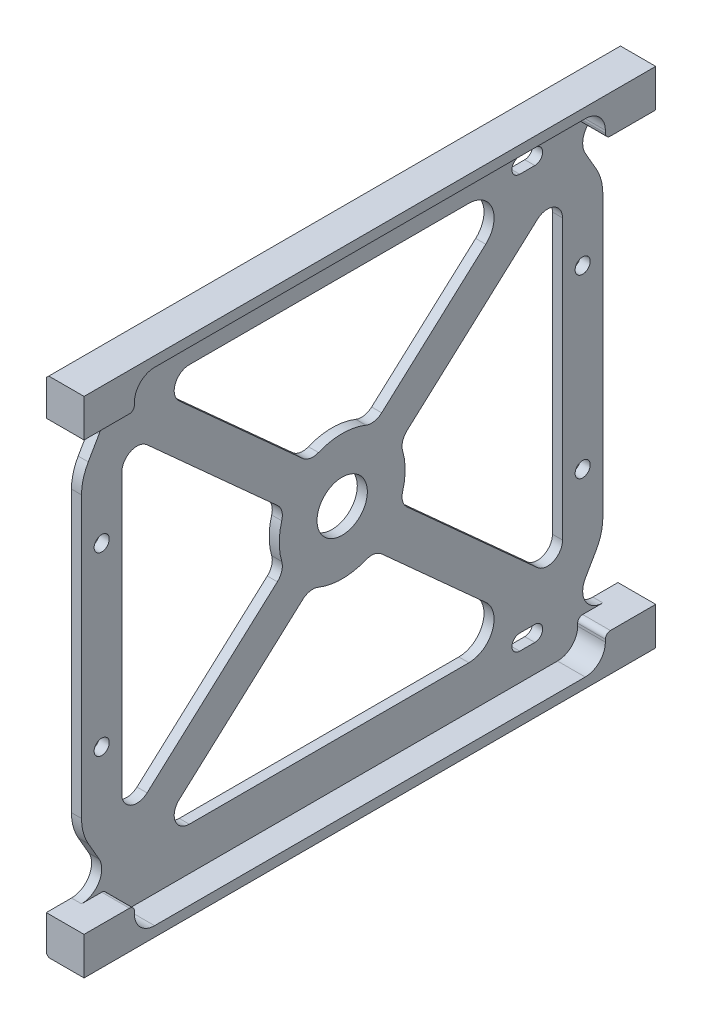
SolidWorks part; units mm, degrees
material "6061-T6 (SS)"
ref_plane "Front Plane" through (0, 0, 0) normal (0, 0, 1) x (1, 0, 0)
ref_plane "Top Plane" through (0, 0, 0) normal (0, 1, 0) x (1, 0, 0)
ref_plane "Right Plane" through (0, 0, 0) normal (1, 0, 0) x (0, 0, -1)
sketch "Sketch1" plane through (0, 0, 0) normal (0, 0, 1) x (1, 0, 0)
  line L0 (0, 50) -> (0, -50)
  line L1 (0, -50) -> (7.5, -50)
  line L2 (7.5, -50) -> (7.5, -42.5)
  line L3 (7.5, -42.5) -> (2, -42.5)
  line L4 (2, -42.5) -> (2, 42.5)
  line L5 (2, 42.5) -> (7.5, 42.5)
  line L6 (7.5, 42.5) -> (7.5, 50)
  line L7 (7.5, 50) -> (0, 50)
  dimension "D1" = 2
  dimension "D2" = 7.5
  dimension "D3" = 7.5
  dimension "D4" = 100
  dimension "D5" = 50
extrude "Boss-Extrude1" add sketch "Sketch1" along normal mid plane 113.5
sketch "Sketch2" plane through (2, 0, 0) normal (1, 0, 0) x (0, 0, -1)
  line L0 (-56.75, -42.5) -> (56.75, -42.5) construction
  line L1 (-56.75, 42.5) -> (-51.75, 42.5)
  line L2 (-56.75, 42.5) -> (-56.75, -42.5)
  line L3 (-56.75, -42.5) -> (-51.75, -42.5)
  line L4 (-51.75, 42.5) -> (-51.75, -42.5)
  line L5 (-56.75, 42.5) -> (-51.75, -42.5) construction
  line L6 (-56.75, -42.5) -> (-51.75, 42.5) construction
  line L7 (-56.75, -42.5) -> (56.75, -42.5) construction
  line L8 (56.75, 42.5) -> (51.75, 42.5)
  line L9 (56.75, 42.5) -> (56.75, -42.5)
  line L10 (56.75, -42.5) -> (51.75, -42.5)
  line L11 (51.75, 42.5) -> (51.75, -42.5)
  line L12 (56.75, 42.5) -> (51.75, -42.5) construction
  line L13 (56.75, -42.5) -> (51.75, 42.5) construction
  line L14 (47.75, 42.5) -> (47.75, -42.5) construction
  line L15 (-56.75, 42.5) -> (56.75, 42.5) construction
  line L16 (-47.75, 42.5) -> (-47.75, -42.5) construction
  line L17 (-56.75, 42.5) -> (56.75, 42.5) construction
  circle A0 centre (-47.75, 17.5) radius 1.5
  circle A1 centre (-47.75, -17.5) radius 1.5
  circle A2 centre (47.75, 17.5) radius 1.5
  circle A3 centre (47.75, -17.5) radius 1.5
  point P4 (-54.25, 0)
  point P12 (54.25, 0)
  line M1 (56.75, -42.5) -> (56.75, 42.5)
  line M2 (56.75, 42.5) -> (-56.75, 42.5)
  line M3 (-56.75, 42.5) -> (-56.75, -42.5)
  line M4 (-56.75, -42.5) -> (56.75, -42.5)
  dimension "D3" = 3
  dimension "D1" = 5
  dimension "D2" = 5
  dimension "D4" = 35
  dimension "D5" = 35
  dimension "D6" = 85
  dimension "D7" = 25
  dimension "D8" = 25
  dimension "D9" = 4
  dimension "D10" = 4
extrude "Cut-Extrude1" cut sketch "Sketch2" against normal blind 2 contours L4 M2 M3 M4 | L11 M2 M4 M1 | L14 A2 | L14 A2 | L14 A3 | L14 A3 | L16 A1 | L16 A1 | L16 A0 | L16 A0
sketch "Sketch3" plane through (2, 0, 0) normal (1, 0, 0) x (0, 0, -1)
  line L1 (-30.3546, -39.5) -> (25.155, -39.5)
  line L2 (-43.75, -27.6973) -> (-43.75, 27.6973)
  line L3 (-30.3546, 39.5) -> (25.155, 39.5)
  line L4 (43.75, -27.6973) -> (43.75, 27.6973)
  line L5 (-43.75, -39.5) -> (43.75, 39.5) construction
  line L6 (-43.75, 39.5) -> (34.7864, -31.4072) construction
  line L7 (-32.365, 34.2733) -> (-7.8435, 12.1338)
  line L8 (-38.7396, 29.924) -> (-12.8695, 6.567)
  line L9 (28.5056, 30.7888) -> (7.8435, 12.1338)
  line L10 (38.7396, 29.924) -> (12.8695, 6.567)
  line L11 (-51.75, 42.5) -> (-51.75, -42.5)
  line L12 (-51.75, -42.5) -> (51.75, -42.5)
  line L13 (51.75, -42.5) -> (51.75, 42.5)
  line L14 (51.75, 42.5) -> (-51.75, 42.5)
  line L15 (-51.75, 42.5) -> (-51.75, -42.5) construction
  line L16 (-51.75, -42.5) -> (51.75, -42.5) construction
  line L17 (51.75, -42.5) -> (51.75, 42.5) construction
  line L18 (51.75, 42.5) -> (-51.75, 42.5) construction
  line L19 (38.7396, -29.924) -> (12.8695, -6.567)
  line L20 (28.5056, -30.7888) -> (7.8435, -12.1338)
  line L21 (-32.365, -34.2733) -> (-7.8435, -12.1338)
  line L22 (-38.7396, -29.924) -> (-12.8695, -6.567)
  line L23 (51.75, -42.5) -> (56.75, -42.5) construction
  line L24 (-43.75, 39.5) -> (13.3825, 39.5) construction
  line L25 (-43.75, 39.5) -> (-43.75, -39.5) construction
  line L26 (-43.75, -39.5) -> (13.3825, -39.5) construction
  line L27 (43.75, 39.5) -> (43.75, -39.5) construction
  line L28 (32.1175, -39.5) -> (43.75, -39.5) construction
  line L30 (32.1175, 39.5) -> (43.75, 39.5) construction
  line L31 (35.25, -41) -> (38.25, -41) construction
  line L32 (35.25, -39.45) -> (38.25, -39.45)
  line L33 (35.25, -42.55) -> (38.25, -42.55)
  line L34 (35.25, 41) -> (38.25, 41) construction
  line L35 (35.25, 42.55) -> (38.25, 42.55)
  line L36 (35.25, 39.45) -> (38.25, 39.45)
  arc A0 (12.8695, 6.567) -> (11.9999, 3.5003) centre (14.8799, 4.3403) ccw
  circle A1 centre (47.75, 17.5) radius 1.5 construction
  arc A2 (11.9999, -3.5003) -> (12.8695, -6.567) centre (14.8799, -4.3403) ccw
  circle A3 centre (0, 0) radius 5
  arc A4 (-11.9999, 3.5003) -> (-11.9999, -3.5003) centre (0, 0) ccw
  arc A5 (4.7041, 11.5811) -> (-4.7041, 11.5811) centre (0, 0) ccw
  arc A6 (11.9999, -3.5003) -> (11.9999, 3.5003) centre (0, 0) ccw
  arc A7 (-4.7041, -11.5811) -> (4.7041, -11.5811) centre (0, 0) ccw
  circle A8 centre (-47.75, -17.5) radius 1.5 construction
  arc A9 (7.8435, -12.1338) -> (4.7041, -11.5811) centre (5.8331, -14.3605) ccw
  arc A10 (-4.7041, -11.5811) -> (-7.8435, -12.1338) centre (-5.8331, -14.3605) ccw
  arc A11 (-11.9999, -3.5003) -> (-12.8695, -6.567) centre (-14.8799, -4.3403) cw
  arc A12 (-11.9999, 3.5003) -> (-12.8695, 6.567) centre (-14.8799, 4.3403) ccw
  arc A13 (7.8435, 12.1338) -> (4.7041, 11.5811) centre (5.8331, 14.3605) cw
  arc A14 (-4.7041, 11.5811) -> (-7.8435, 12.1338) centre (-5.8331, 14.3605) cw
  arc A16 (43.75, 27.6973) -> (38.7396, 29.924) centre (40.75, 27.6973) ccw
  arc A17 (43.75, -27.6973) -> (38.7396, -29.924) centre (40.75, -27.6973) cw
  arc A19 (-30.3546, -39.5) -> (-32.365, -34.2733) centre (-30.3546, -36.5) cw
  arc A20 (-38.7396, -29.924) -> (-43.75, -27.6973) centre (-40.75, -27.6973) cw
  arc A21 (-43.75, 27.6973) -> (-38.7396, 29.924) centre (-40.75, 27.6973) cw
  arc A22 (-30.3546, 39.5) -> (-32.365, 34.2733) centre (-30.3546, 36.5) ccw
  arc A31 (35.25, -39.45) -> (35.25, -42.55) centre (35.25, -41) ccw
  arc A32 (38.25, -42.55) -> (38.25, -39.45) centre (38.25, -41) ccw
  arc A33 (35.25, 42.55) -> (35.25, 39.45) centre (35.25, 41) ccw
  arc A34 (38.25, 39.45) -> (38.25, 42.55) centre (38.25, 41) ccw
  arc A35 (25.155, -39.5) -> (28.5056, -30.7888) centre (25.155, -34.5) ccw
  arc A36 (28.5056, 30.7888) -> (25.155, 39.5) centre (25.155, 34.5) ccw
  point P0 (0, 0)
  point P40 (11.3636, -5.2075)
  point P45 (-6.3376, -10.7743)
  point P52 (6.3376, 10.7743)
  point P78 (36.75, -41)
  point P96 (36.75, 41)
  dimension "D7" = 10
  dimension "D11" = 3
  dimension "D12" = 5
  dimension "D13" = 3
  dimension "D3" = 4
  dimension "D6" = 4
  dimension "D8" = 7.5
  dimension "D9" = 7.5
  dimension "D10" = 7.5
  dimension "D4" = 4
  dimension "D5" = 3
  dimension "D14" = 3.1
  dimension "D17" = 3
  dimension "D19" = 82
  dimension "D20" = 41
  dimension "D23" = 88.5
  dimension "D24" = 88.5
extrude "Cut-Extrude2" cut sketch "Sketch3" against normal through all
chamfer "Chamfer1" distance 0.5 angle 45 2 edges at (0, 50, 0) (0, -50, 0)
sketch "Sketch4" plane through (7.5, 0, 0) normal (1, 0, 0) x (0, 0, -1)
  line L5 (-56.75, -42.5) -> (56.75, -42.5) construction
  line L6 (-56.75, 42.5) -> (56.75, 42.5) construction
  line L7 (-51.75, -42.5) -> (34.8595, -42.5) construction
  line L12 (-46.75, 43.5) -> (-46.75, 44)
  line L13 (-42.75, 48) -> (42.75, 48)
  line L14 (-56.75, -42.5) -> (-47.75, -42.5)
  line L15 (-56.75, 42.5) -> (-47.75, 42.5)
  line L16 (46.75, 44) -> (46.75, 43.5)
  line L17 (46.75, -43.5) -> (46.75, -44)
  line L18 (42.75, -48) -> (-42.75, -48)
  line L19 (-46.75, -44) -> (-46.75, -43.5)
  line L20 (-56.75, 50) -> (56.75, 50) construction
  line L21 (-56.75, -50) -> (56.75, -50) construction
  line L22 (47.75, 42.5) -> (56.75, 42.5)
  line L23 (47.75, -42.5) -> (56.75, -42.5)
  line L24 (-47.75, 42.5) -> (47.75, 42.5)
  line L25 (47.75, -42.5) -> (-47.75, -42.5)
  arc A0 (47.75, 42.5) -> (46.75, 43.5) centre (47.75, 43.5) cw
  arc A1 (-46.75, 43.5) -> (-47.75, 42.5) centre (-47.75, 43.5) cw
  arc A2 (47.75, -42.5) -> (46.75, -43.5) centre (47.75, -43.5) ccw
  arc A3 (-46.75, -43.5) -> (-47.75, -42.5) centre (-47.75, -43.5) ccw
  arc A4 (-42.75, -48) -> (-46.75, -44) centre (-42.75, -44) cw
  arc A5 (42.75, -48) -> (46.75, -44) centre (42.75, -44) ccw
  arc A6 (46.75, 44) -> (42.75, 48) centre (42.75, 44) ccw
  arc A7 (-42.75, 48) -> (-46.75, 44) centre (-42.75, 44) ccw
  point P24 (46.75, 42.5)
  point P27 (-46.75, 42.5)
  point P30 (46.75, -42.5)
  point P33 (-46.75, -42.5)
  line M16 (-56.75, 42.5) -> (56.75, 42.5)
  dimension "D11" = 1
  dimension "D12" = 4
  dimension "D6" = 5
  dimension "D7" = 5
  dimension "D8" = 5
  dimension "D9" = 2
  dimension "D10" = 2
extrude "Cut-Extrude3" cut sketch "Sketch4" against normal up to surface (5.5 mm away) contours L18 A5 L17 A2 L25 A3 L19 A4 | L13 A7 L12 A1 A0 L16 A6 M16 up to face at (2, 0, 26.9729)
sketch "Sketch5" plane through (0, 0, 0) normal (-1, 0, 0) x (0, 0, 1)
  line L0 (-56.75, 42.5) -> (-51.75, 42.5) construction
  line L5 (-50.4103, 32.8205) -> (-48.2859, 36.5)
  line L6 (-51.75, 42.5) -> (-51.75, -42.5) construction
  line L17 (-51.75, 42.5) -> (-51.75, 23.7514)
  line L19 (-51.75, -42.5) -> (-56.75, -42.5) construction
  line L25 (-48.2859, -36.5) -> (-50.4103, -32.8205)
  line L27 (-51.75, -23.3339) -> (-51.75, -42.5)
  line L30 (-51.75, 27.8205) -> (-51.75, -27.8205)
  arc A0 (-51.75, -42.5) -> (-48.2859, -36.5) centre (-51.75, -38.5) ccw
  arc A1 (-48.2859, 36.5) -> (-51.75, 42.5) centre (-51.75, 38.5) ccw
  arc A4 (-50.4103, -32.8205) -> (-51.75, -27.8205) centre (-41.75, -27.8205) cw
  arc A5 (-50.4103, 32.8205) -> (-51.75, 27.8205) centre (-41.75, 27.8205) ccw
  point P1 (0, 0)
  point P5 (0, 0)
  point P9 (0, 0)
  point P10 (0, 0)
  point P11 (0, 0)
  point P13 (0, 0)
  dimension "D2" = 4
  dimension "D5" = 30
  dimension "D6" = 10
  dimension "D1" = 30
extrude "Cut-Extrude4" cut sketch "Sketch5" against normal blind 10
mirror "Mirror1" about plane through (0, 0, 0) normal (0, 0, 1) of "Cut-Extrude4"
equation "\"D3@Sketch1\"=\"D2@Sketch1\""
equation "\"D5@Sketch1\"=\"D4@Sketch1\"/2"
equation "\"D5@Sketch2\"=\"D4@Sketch2\""
equation "\"D7@Sketch2\"=(\"D6@Sketch2\"-\"D4@Sketch2\")/2"
equation "\"D8@Sketch2\"=\"D7@Sketch2\""
equation "\"D10@Sketch2\"=\"D9@Sketch2\""
equation "\"D6@Sketch3\"=\"D4@Sketch3\""
equation "\"D9@Sketch3\"=\"D8@Sketch3\""
equation "\"D10@Sketch3\"=\"D8@Sketch3\""
equation "\"D4@Sketch3\"=\"D3@Sketch3\""
equation "\"D6@Sketch4\"=\"D5@Sketch4\""
equation "\"D7@Sketch4\"=\"D5@Sketch4\""
equation "\"D8@Sketch4\"=\"D7@Sketch4\""
equation "\"D10@Sketch4\"=\"D9@Sketch4\""
equation "\"D20@Sketch3\"=\"D19@Sketch3\"/2"
equation "\"D24@Sketch3\"=\"D23@Sketch3\""
